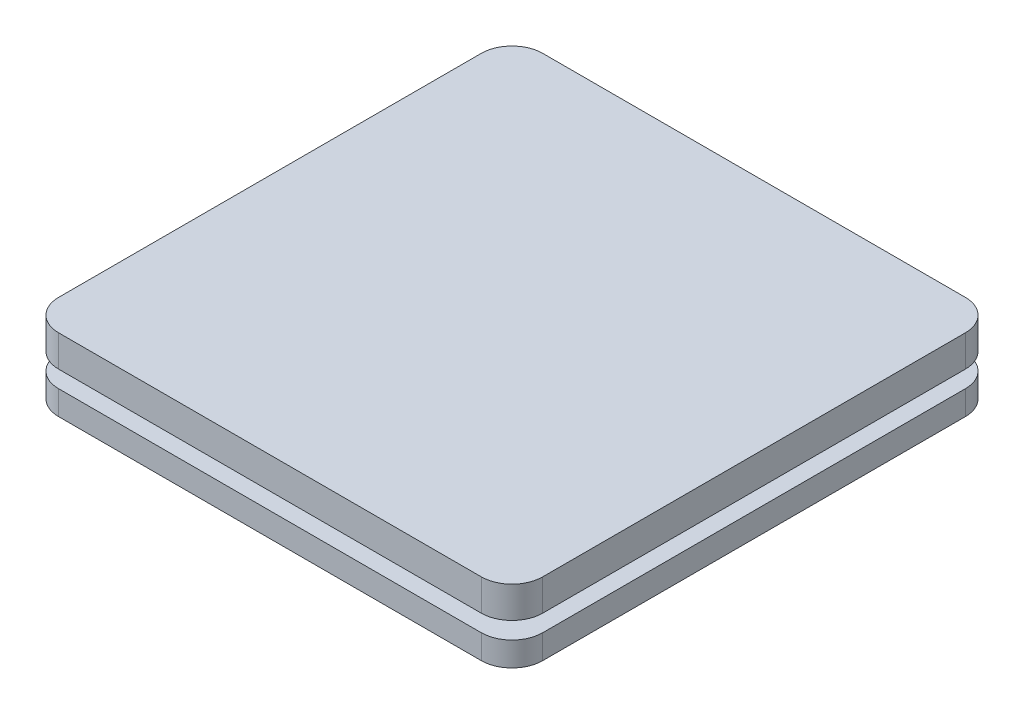
SolidWorks part; units mm, degrees
ref_plane "Front Plane" through (0, 0, 0) normal (0, 0, 1) x (1, 0, 0)
ref_plane "Top Plane" through (0, 0, 0) normal (0, 1, 0) x (1, 0, 0)
ref_plane "Right Plane" through (0, 0, 0) normal (1, 0, 0) x (0, 0, -1)
sketch "Sketch1" plane through (0, 0, 0) normal (0, 1, 0) x (1, 0, 0)
  line L1 (-50, 50) -> (50, 50)
  line L2 (-50, 50) -> (-50, -50)
  line L3 (-50, -50) -> (50, -50)
  line L4 (50, 50) -> (50, -50)
  point P4 (0, 50)
  point P5 (50, 0)
  dimension "D1" = 100
extrude "Boss-Extrude1" add sketch "Sketch1" along normal blind 6.5
ref_plane "Plane1" through (0, -3.5, 0) normal (0, -1, 0) x (-1, 0, 0)
sketch "Sketch2" plane through (0, -3.5, 0) normal (0, -1, 0) x (-1, 0, 0)
  line L4 (50, -50) -> (50, 50)
  line L5 (50, 50) -> (-50, 50)
  line L6 (-50, 50) -> (-50, -50)
  line L7 (-50, -50) -> (50, -50)
  line L8 (50, -50) -> (50, 50)
  line L9 (50, 50) -> (-50, 50)
  line L10 (-50, 50) -> (-50, -50)
  line L11 (-50, -50) -> (50, -50)
  dimension "D1" = 0
extrude "Boss-Extrude2" add sketch "Sketch2" along normal blind 5 separate body
sketch "Sketch3" plane through (0, -8.5, 0) normal (0, -1, 0) x (1, 0, 0)
  line L4 (50, 50) -> (-50, 50)
  line L5 (-50, 50) -> (-50, -50)
  line L6 (-50, -50) -> (50, -50)
  line L7 (50, -50) -> (50, 50)
  line L8 (50, 50) -> (-50, 50)
  line L9 (-50, 50) -> (-50, -50)
  line L10 (-50, -50) -> (50, -50)
  line L11 (50, -50) -> (50, 50)
  dimension "D1" = 0
extrude "Boss-Extrude3" add sketch "Sketch3" along normal blind 5
sketch "Sketch4" plane through (0, 0, 50) normal (0, 0, 1) x (1, 0, 0)
  line L0 (-25, -13.5) -> (-25, -8.5)
  line L1 (50, -13.5) -> (-50, -13.5) construction
  line L2 (-25, -8.5) -> (-5, -8.5)
  line L3 (-5, -8.5) -> (-7.8868, -13.5)
  line L4 (-7.8868, -13.5) -> (-25, -13.5)
  dimension "D1" = 20
  dimension "D2" = 5
  dimension "D3" = 60
  dimension "D4" = 5
extrude "Cut-Extrude1" cut sketch "Sketch4" against normal through all
mirror "Mirror1" about plane through (0, 0, 0) normal (1, 0, 0) of "Cut-Extrude1"
ref_plane "Plane2" through (0, 2.5, 0) normal (0, 1, 0) x (1, 0, 0)
sketch "Sketch6" plane through (0, -13.5, 0) normal (0, -1, 0) x (1, 0, 0)
  line L0 (-50, 50) -> (-50, -50) construction
  line L1 (45, -45) -> (-45, -45)
  line L2 (45, -45) -> (45, 45)
  line L3 (45, 45) -> (-45, 45)
  line L4 (-45, -45) -> (-45, 45)
  line L5 (50, -50) -> (50, 50) construction
  line L6 (-7.8868, -50) -> (7.8868, -50) construction
  line L7 (7.8868, 50) -> (-7.8868, 50) construction
  line L9 (50, -50) -> (-50, -50)
  line L10 (50, -50) -> (50, 50)
  line L11 (50, 50) -> (-50, 50)
  line L12 (-50, -50) -> (-50, 50)
  dimension "D1" = 5
  dimension "D2" = 5
  dimension "D3" = 5
  dimension "D4" = 5
extrude "Cut-Extrude2" cut sketch "Sketch6" against normal up to surface (5 mm away) up to face at (15, -8.5, 0)
sketch "Sketch8" plane through (0, -13.5, 0) normal (0, -1, 0) x (-1, 0, 0)
  line L0 (0, -32) -> (0, 32) construction
  line L1 (32, -32) -> (-32, -32) construction
  line L2 (32, -32) -> (32, 32) construction
  line L3 (32, 32) -> (-32, 32) construction
  line L4 (-32, -32) -> (-32, 32) construction
  line L5 (32, 0) -> (-32, 0) construction
  point P9 (0, 0)
  dimension "D1" = 32
  dimension "D2" = 32
sketch "Sketch9" plane through (0, 0, 0) normal (0, -1, 0) x (1, 0, 0)
  line L1 (-35, 35) -> (35, 35)
  line L2 (-35, 35) -> (-35, -35)
  line L3 (-35, -35) -> (35, -35)
  line L4 (35, 35) -> (35, -35)
  line L5 (50, 50) -> (50, -50) construction
  point P4 (0, 35)
  point P9 (35, 0)
  dimension "D1" = 15
extrude "Boss-Extrude4" add sketch "Sketch9" along normal up to next
hole_wizard "CBORE for M5 Cheese Head Screw1" positions "Sketch10" profile "Sketch11" counterbore size "M5" standard "ISO"
sketch "Sketch10" plane through (0, -13.5, 0) normal (0, -1, 0) x (-1, 0, 0)
  point P0 (-32, 32)
  point P3 (0, 32)
  point P6 (32, 32)
  point P9 (32, -32)
  point P12 (0, -32)
  point P15 (-32, -32)
sketch "Sketch11" plane through (32, -13.5, -32) normal (1, 0, 0) x (0, 0, -1)
  line L0 (0, 0) -> (0, 12.001)
  line L1 (0, 12.001) -> (1.666, 11)
  line L2 (1.666, 11) -> (1.666, 5)
  line L3 (1.666, 5) -> (4, 5)
  line L4 (4, 5) -> (4, 0)
  line L5 (4, 0) -> (0, 0)
  line L10 (0, 12.001) -> (-1.666, 11) construction
  line L11 (0, -6.35) -> (0, 107.95) construction
  dimension "Hole Dia." = 3.332
  dimension "Hole Depth" = 11
  dimension "C'Bore Dia." = 8
  dimension "C'Bore Depth" = 5
  dimension "Drill Angle" = 118
fillet "Fillet1" radius 6.35 8 edges at (50, -6, 50) (50, 3.25, 50) (-50, -6, 50) (-50, 3.25, 50) (-50, -6, -50) (-50, 3.25, -50) (50, -6, -50) (50, 3.25, -50)
chamfer "Chamfer1" distance 6.35 angle 45 4 edges at (45, -11, 45) (-45, -11, 45) (-45, -11, -45) (45, -11, -45)
sketch "Sketch14" plane through (0, -13.5, 0) normal (0, -1, 0) x (1, 0, 0)
  line L0 (-50, -43.65) -> (-50, 43.65) construction
  line L1 (-50, 25) -> (-25, 25)
  line L2 (-50, 25) -> (-50, -25)
  line L3 (-50, -25) -> (-25, -25)
  line L4 (-25, 25) -> (-25, -25)
  line L5 (-25, -45) -> (-25, 45) construction
  point P8 (-50, 0)
  dimension "D1" = 50
extrude "Cut-Extrude3" cut sketch "Sketch14" against normal up to surface (5 mm away) up to face at (-36.2167, -8.5, 0)
mirror "Mirror2" about plane through (0, 0, 0) normal (1, 0, 0) of "Cut-Extrude3"
